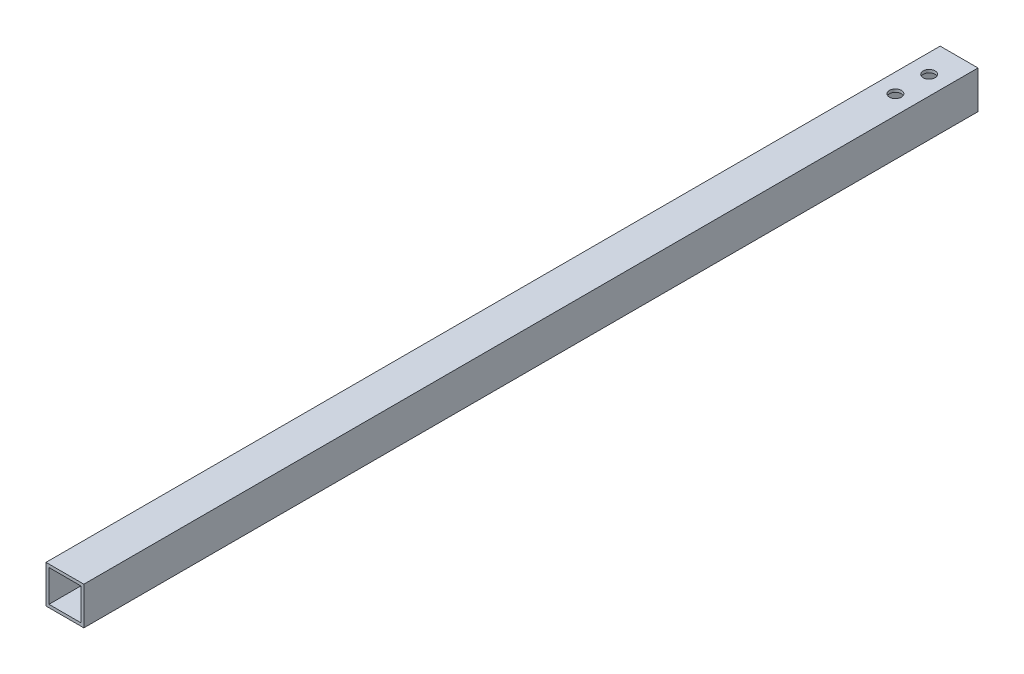
SolidWorks part; units mm, degrees
ref_plane "Front Plane" through (0, 0, 0) normal (0, 0, 1) x (1, 0, 0)
ref_plane "Top Plane" through (0, 0, 0) normal (0, 1, 0) x (1, 0, 0)
ref_plane "Right Plane" through (0, 0, 0) normal (1, 0, 0) x (0, 0, -1)
sketch "Sketch1" plane through (0, 0, 0) normal (0, 0, 1) x (1, 0, 0)
  line L1 (-5.9161, 5.049) -> (6.7839, 5.049)
  line L2 (-5.9161, 5.049) -> (-5.9161, -7.651)
  line L3 (-5.9161, -7.651) -> (6.7839, -7.651)
  line L4 (6.7839, 5.049) -> (6.7839, -7.651)
  point P4 (0, 0)
  dimension "D1" = 12.7
  dimension "D2" = 12.7
extrude "Boss-Extrude1" add sketch "Sketch1" along normal blind 300 contours L4 L3 L2 L1
shell "Shell18" thickness 1
sketch "Sketch2" plane through (0, 5.049, 0) normal (0, 1, 0) x (1, 0, 0)
  circle A0 centre (0.4339, -10.04) radius 2
  circle A1 centre (0.4339, -21.3485) radius 2
extrude "Cut-Extrude1" cut sketch "Sketch2" against normal blind 30
sketch "Sketch3" plane through (0, 5.049, 0) normal (0, 1, 0) x (1, 0, 0)
  circle A0 centre (0.4339, -336) radius 2
  circle A1 centre (0.4339, -316) radius 2
  dimension "D2" = 20
extrude "Cut-Extrude2" cut sketch "Sketch3" against normal blind 20
